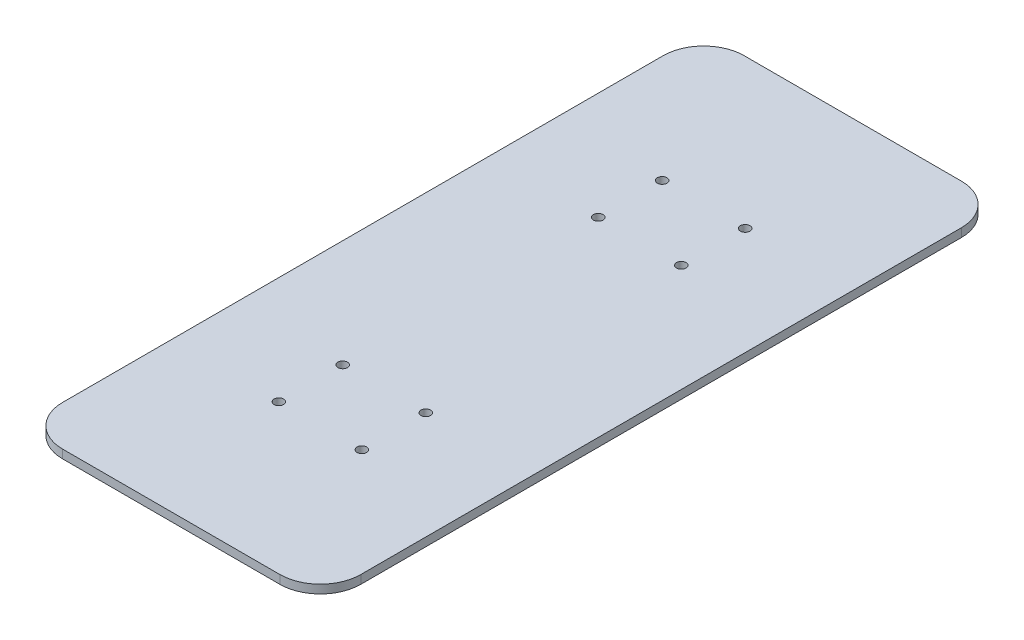
SolidWorks part; units mm, degrees
ref_plane "Front Plane" through (0, 0, 0) normal (0, 0, 1) x (1, 0, 0)
ref_plane "Top Plane" through (0, 0, 0) normal (0, 1, 0) x (1, 0, 0)
ref_plane "Right Plane" through (0, 0, 0) normal (1, 0, 0) x (0, 0, -1)
sketch "Sketch1" plane through (0, 0, 0) normal (0, 1, 0) x (1, 0, 0)
  line L1 (0, 0) -> (140, 0)
  line L2 (0, 0) -> (0, 320)
  line L3 (0, 320) -> (140, 320)
  line L4 (140, 0) -> (140, 320)
  dimension "D1" = 140
  dimension "D2" = 320
extrude "Boss-Extrude1" add sketch "Sketch1" along normal blind 4
sketch "Sketch2" plane through (0, 4, 0) normal (0, 1, 0) x (1, 0, 0)
  line L0 (70, 320) -> (70, 0) construction
  line L1 (140, 320) -> (0, 320) construction
  line L2 (0, 0) -> (140, 0) construction
  line L3 (89.5, 250) -> (89.5, 220) construction
  line L4 (140, 160) -> (0, 160) construction
  line L5 (140, 0) -> (140, 320) construction
  line L6 (0, 320) -> (0, 0) construction
  line L7 (89.5, 220) -> (89.5, 160) construction
  line L8 (89.5, 160) -> (89.5, 100) construction
  line L9 (89.5, 100) -> (89.5, 70) construction
  circle A0 centre (89.5, 250) radius 2.25
  circle A1 centre (89.5, 220) radius 2.25
  circle A2 centre (89.5, 100) radius 2.25
  circle A3 centre (89.5, 70) radius 2.25
  circle A4 centre (50.5, 70) radius 2.25
  circle A5 centre (50.5, 100) radius 2.25
  circle A6 centre (50.5, 220) radius 2.25
  circle A7 centre (50.5, 250) radius 2.25
  dimension "D1" = 4.5
  dimension "D2" = 30
  dimension "D3" = 60
  dimension "D4" = 19.5
extrude "Cut-Extrude1" cut sketch "Sketch2" against normal up to next
fillet "Fillet1" radius 19 4 edges at (0, 2, -320) (140, 2, -320) (140, 2, 0) (0, 2, 0)
